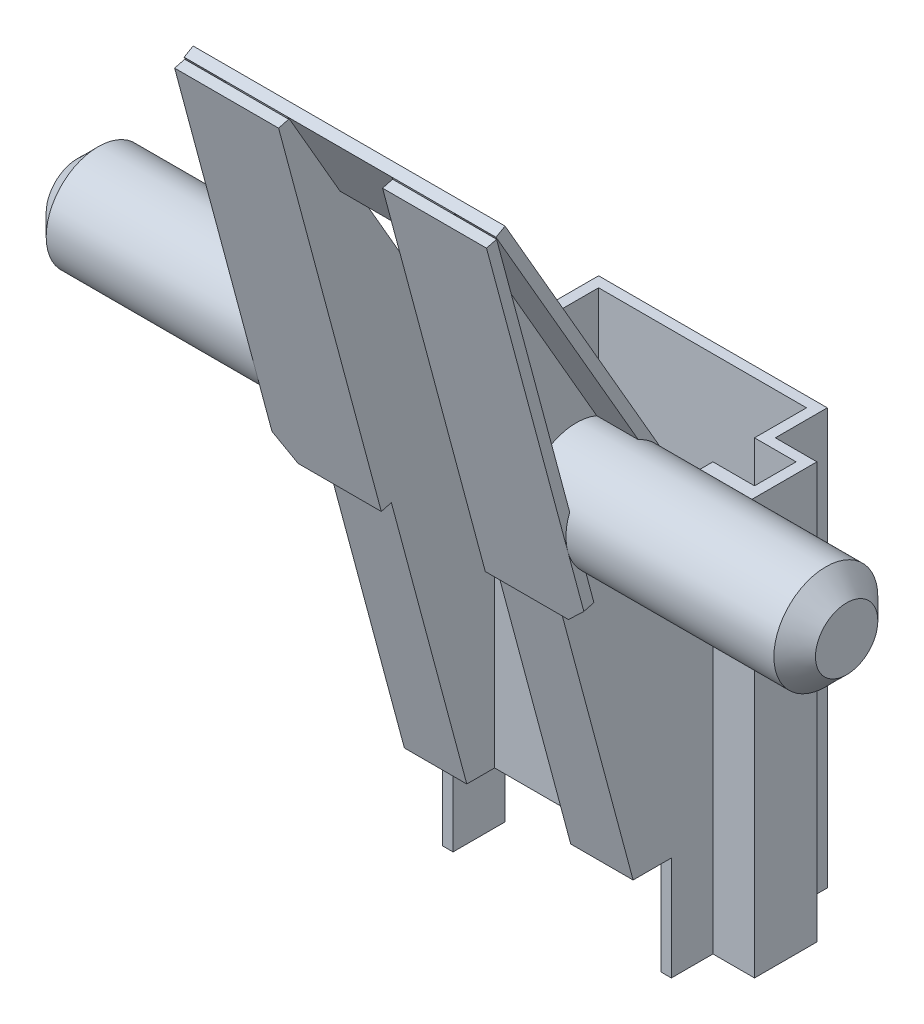
SolidWorks part; units mm, degrees
ref_plane "Ebene vorne" through (0, 0, 0) normal (0, 0, 1) x (1, 0, 0)
ref_plane "Ebene oben" through (0, 0, 0) normal (0, 1, 0) x (1, 0, 0)
ref_plane "Ebene rechts" through (0, 0, 0) normal (1, 0, 0) x (0, 0, -1)
sketch "Skizze1" plane through (0, 0, 0) normal (0, 1, 0) x (1, 0, 0)
  line L0 (-5, 1) -> (-5, 3.5)
  line L1 (5, -3.5) -> (-5, -3.5)
  line L2 (5, -3.5) -> (5, -1)
  line L3 (5, 3.5) -> (-5, 3.5)
  line L4 (-5, -3.5) -> (-5, -1)
  line L5 (5, -3.5) -> (-5, 3.5) construction
  line L6 (5, 3.5) -> (-5, -3.5) construction
  line L7 (7, -1) -> (5, -1)
  line L8 (7, -1) -> (7, 1)
  line L9 (7, 1) -> (5, 1)
  line L10 (-7, -1) -> (-7, 1)
  line L11 (7, -1) -> (-7, 1) construction
  line L12 (7, 1) -> (-7, -1) construction
  line L13 (5.5, -4) -> (-5.5, -4)
  line L14 (7.5, -1.5) -> (7.5, 1.5)
  line L15 (5.5, 4) -> (-5.5, 4)
  line L16 (-7.5, -1.5) -> (-7.5, 1.5)
  line L17 (5.5, -3.04) -> (-5.5, 3.04) construction
  line L18 (5.5, 3.04) -> (-5.5, -3.04) construction
  line L19 (-5, 1) -> (-7, 1)
  line L20 (5, 1) -> (5, 3.5)
  line L21 (-5, -1) -> (-7, -1)
  line L25 (-7.5, 1.5) -> (-5.5, 1.5)
  line L26 (-5.5, 4) -> (-5.5, 1.5)
  line L29 (7.5, 1.5) -> (5.5, 1.5)
  line L30 (5.5, 4) -> (5.5, 1.5)
  line L33 (7.5, -1.5) -> (5.5, -1.5)
  line L34 (5.5, -4) -> (5.5, -1.5)
  line L37 (-7.5, -1.5) -> (-5.5, -1.5)
  line L38 (-5.5, -4) -> (-5.5, -1.5)
  point P0 (0, 0)
  point P5 (0, 0)
  point P11 (0, 0)
  dimension "D1" = 10
  dimension "D2" = 2
  dimension "D3" = 14
  dimension "D4" = 0.5
  dimension "D5" = 0.5
  dimension "D6" = 7
  dimension "D7" = 0.5
  dimension "D8" = 0.5
  dimension "D9" = 0.5
  dimension "D10" = 0.5
  dimension "D11" = 0.5
  dimension "D12" = 0.5
extrude "Aufsatz-Linear austragen1" add sketch "Skizze1" along normal blind 20
sketch "Skizze2" plane through (-7.5, 0, 0) normal (-1, 0, 0) x (0, 0, 1)
  line L3 (13.5, 37.3205) -> (13.933, 37.0705)
  line L7 (3.5, 20) -> (13.5, 37.3205)
  line L13 (3.5, 20) -> (1.5, 20)
  line L18 (4, 20) -> (4, 0) construction
  line L20 (4, 19.866) -> (13.933, 37.0705)
  line L21 (1.5, 20) -> (1.5, 19.499)
  line L22 (1.5, 20) -> (1.5, 0) construction
  line L23 (1.5, 19.499) -> (4, 19.499)
  line L24 (4, 19.499) -> (4, 19.866)
  dimension "D1" = 0.5
  dimension "D2" = 0.5
  dimension "D4" = 20
extrude "Aufsatz-Linear austragen2" add sketch "Skizze2" against normal up to vertex (15 mm away)
sketch "Skizze6" plane through (-5.5, 0, 0) normal (-1, 0, 0) x (0, 0, 1)
  line L0 (13.933, 37.0705) -> (4, 0)
  line L1 (4, 0) -> (4, 19.866)
  line L2 (4, 19.866) -> (13.933, 37.0705)
extrude "Aufsatz-Linear austragen4" add sketch "Skizze6" against normal blind 3
sketch "Skizze7" plane through (0, 20, 0) normal (0, 1, 0) x (1, 0, 0)
  line L1 (-5, -1.5) -> (5, -1.5)
  line L2 (-5, -1.5) -> (-5, -3.5)
  line L3 (-5, -3.5) -> (5, -3.5)
  line L4 (5, -1.5) -> (5, -3.5)
  line L5 (5, -1.5) -> (5, -1) construction
  line L6 (7.5, -3.5) -> (-7.5, -3.5) construction
extrude "Schnitt-Linear austragen1" cut sketch "Skizze7" against normal up to next
mirror "Spiegeln3" about plane through (0, 0, 0) normal (1, 0, 0) of "Aufsatz-Linear austragen4"
sketch "Skizze8" plane through (0, 0, 3.5) normal (0, 0, -1) x (-1, 0, 0)
  line L0 (5.5, 20) -> (5.5, 0) construction
  line L1 (-5.5, 0) -> (5.5, 0)
  line L2 (-5.5, 0) -> (-5.5, 5)
  line L3 (-5.5, 5) -> (5.5, 5)
  line L4 (5.5, 0) -> (5.5, 5)
  dimension "D1" = 5
sketch "Skizze11" plane through (0, 3.2345, -5.6022) normal (0, -0.5, 0.866) x (1, 0, 0)
  line L0 (2.5, 39.0705) -> (2.5, 19.2045) construction
  line L1 (-2.5, 19.2045) -> (2.5, 19.2045)
  line L2 (-2.5, 19.2045) -> (-2.5, 34.0705)
  line L3 (-2.5, 34.0705) -> (2.5, 34.0705)
  line L4 (2.5, 19.2045) -> (2.5, 34.0705)
  line L5 (2.5, 39.0705) -> (-2.5, 39.0705) construction
  dimension "D1" = 5
extrude "Schnitt-Linear austragen4" cut sketch "Skizze11" against normal blind 10
sketch "Skizze12" plane through (0, -1, 3.7321) normal (0, -0.2588, 0.9659) x (1, 0, 0)
  line L0 (-2.5, 1.0353) -> (-2.5, 39.4135) construction
  line L1 (-2.5, 39.3135) -> (-7.5, 39.3135)
  line L2 (-2.5, 39.3135) -> (-2.5, 20.2244)
  line L3 (-2.5, 20.2244) -> (-7.5, 20.2244)
  line L4 (-7.5, 39.3135) -> (-7.5, 20.2244)
  line L5 (-2.5, 39.4135) -> (-5.5, 39.4135) construction
  dimension "D1" = 0.1
extrude "Aufsatz-Linear austragen7" add sketch "Skizze12" along normal blind 0.5
mirror "Spiegeln4" about plane through (0, 0, 0) normal (1, 0, 0) of "Aufsatz-Linear austragen7"
sketch "Skizze13" plane through (5.5, 0, 0) normal (1, 0, 0) x (0, 0, -1)
  line L0 (-13.5, 37.3205) -> (-3.5, 20) construction
  line L1 (-14.3901, 36.8445) -> (-9.4495, 18.4058) construction
  circle A0 centre (-8.0693, 22.9143) radius 2.5
  point P2 (-8.0154, 22.8211)
  dimension "D1" = 5
extrude "Aufsatz-Linear austragen8" add sketch "Skizze13" along normal blind 13
extrude "Schnitt-Linear austragen5" cut sketch "Skizze8" against normal blind 13
mirror "Spiegeln5" about plane through (0, 0, 0) normal (1, 0, 0) of "Aufsatz-Linear austragen8"
chamfer "Fase1" distance 1 angle 45 4 edges at (-18.5, 22.9143, 5.5693) (18.5, 22.9143, 5.5693) (7.5, 18.4705, 9.208) (-7.5, 18.4705, 9.208)
